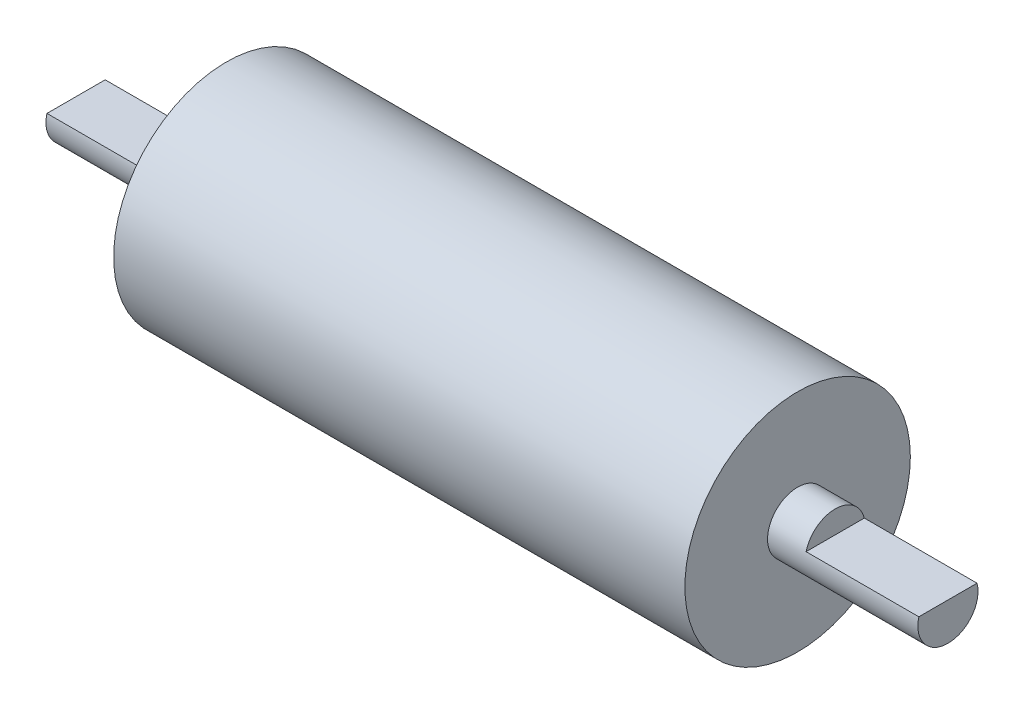
SolidWorks part; units mm, degrees
ref_plane "Plano frontal" through (0, 0, 0) normal (0, 0, 1) x (1, 0, 0)
ref_plane "Plano superior" through (0, 0, 0) normal (0, 1, 0) x (1, 0, 0)
ref_plane "Plano direito" through (0, 0, 0) normal (1, 0, 0) x (0, 0, -1)
sketch "Esboço8" plane through (0, 0, 0) normal (1, 0, 0) x (0, 0, -1)
  circle A0 centre (0, 0) radius 4
  dimension "D1" = 8
extrude "Ressalto-extrusão4" add sketch "Esboço8" along normal blind 20
sketch "Esboço9" plane through (20, 0, 0) normal (1, 0, 0) x (0, 0, -1)
  circle A0 centre (0, 0) radius 15
  dimension "D1" = 30
extrude "Ressalto-extrusão5" add sketch "Esboço9" along normal blind 76
sketch "Esboço10" plane through (96, 0, 0) normal (1, 0, 0) x (0, 0, -1)
  circle A0 centre (0, 0) radius 4
  dimension "D1" = 8
extrude "Ressalto-extrusão6" add sketch "Esboço10" along normal blind 20
sketch "Esboço11" plane through (0, 0, 0) normal (-1, 0, 0) x (0, 0, 1)
  line L2 (-7.6297, 4) -> (7.3486, 4)
  line L3 (-7.6297, 4) -> (-7.6297, 1)
  line L4 (-7.6297, 1) -> (7.3486, 1)
  line L5 (7.3486, 4) -> (7.3486, 1)
  circle A3 centre (0, 0) radius 4 construction
  dimension "D1" = 3
extrude "Corte-extrusão1" cut sketch "Esboço11" against normal blind 15
sketch "Esboço12" plane through (116, 0, 0) normal (1, 0, 0) x (0, 0, -1)
  line L2 (-6.9828, 4) -> (7.2989, 4)
  line L3 (-6.9828, 4) -> (-6.9828, 1)
  line L4 (-6.9828, 1) -> (7.2989, 1)
  line L5 (7.2989, 4) -> (7.2989, 1)
  circle A3 centre (0, 0) radius 4 construction
  dimension "D1" = 3
extrude "Corte-extrusão2" cut sketch "Esboço12" against normal blind 15
